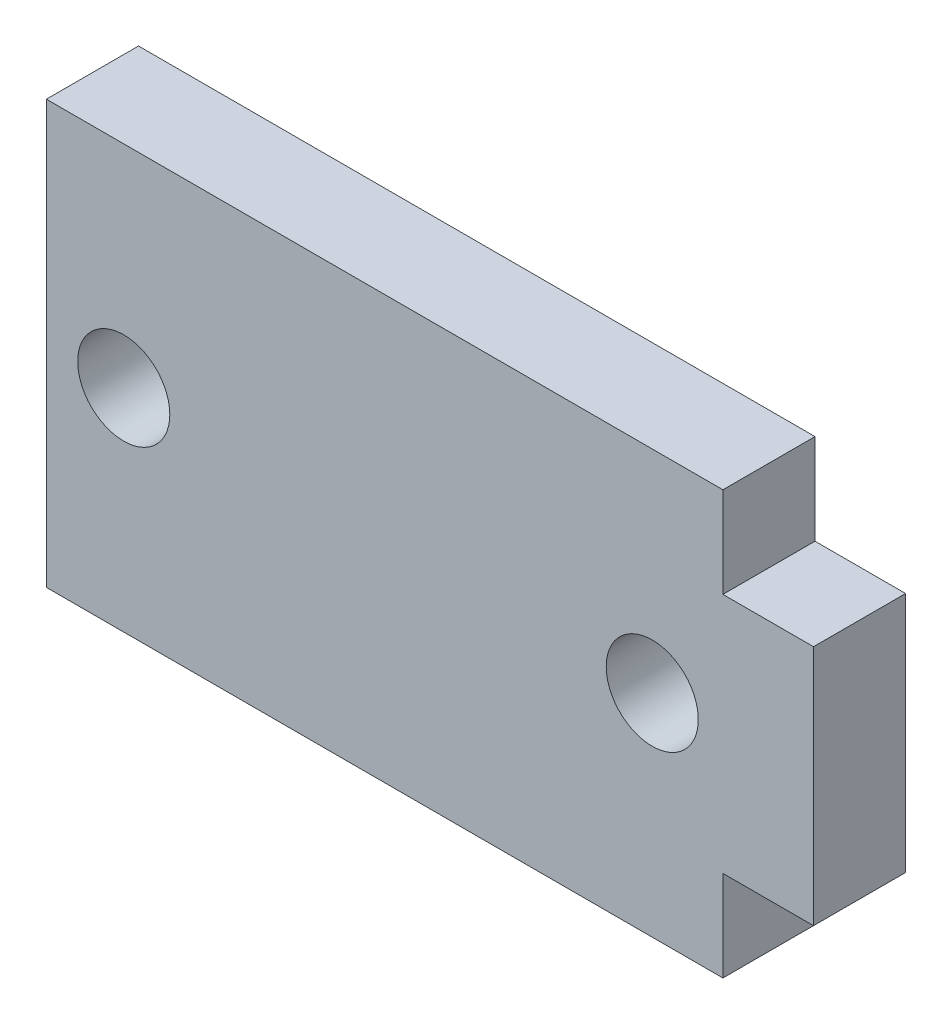
SolidWorks part; units mm, degrees
ref_plane "Front Plane" through (0, 0, 0) normal (0, 0, 1) x (1, 0, 0)
ref_plane "Top Plane" through (0, 0, 0) normal (0, 1, 0) x (1, 0, 0)
ref_plane "Right Plane" through (0, 0, 0) normal (1, 0, 0) x (0, 0, -1)
sketch "Sketch1" plane through (0, 0, 0) normal (0, 0, 1) x (1, 0, 0)
  line L0 (11.2, 18.5) -> (11.2, -13.65) construction
  line L1 (-11.2, 20) -> (11.2, 20)
  line L2 (-11.2, 20) -> (-11.2, 6)
  line L3 (-11.2, 6) -> (11.2, 6)
  line L4 (11.2, 20) -> (11.2, 17)
  line L5 (-11.2, 13) -> (-8.6386, 13) construction
  line L6 (0, 6) -> (0, 9.0681) construction
  line L8 (11.2, 9) -> (14.2, 9)
  line L10 (11.2, 17) -> (14.2, 17)
  line L11 (14.2, 9) -> (14.2, 17)
  line L13 (11.2, 13) -> (12.9118, 13) construction
  line L15 (11.2, 9) -> (11.2, 6)
  circle A0 centre (8.8614, 13) radius 1.525
  circle A1 centre (-8.6386, 13) radius 1.525
  arc A2 (7.4429, 13.6845) -> (8.1658, 14.413) centre (8.8614, 13) ccw construction
  point P9 (-8.6386, 13)
  dimension "D3" = 3.05
  dimension "D4" = 3.05
  dimension "D1" = 14
  dimension "D2" = 22.4
  dimension "D5" = 3
  dimension "D6" = 8
extrude "Boss-Extrude1" add sketch "Sketch1" along normal blind 3.05
